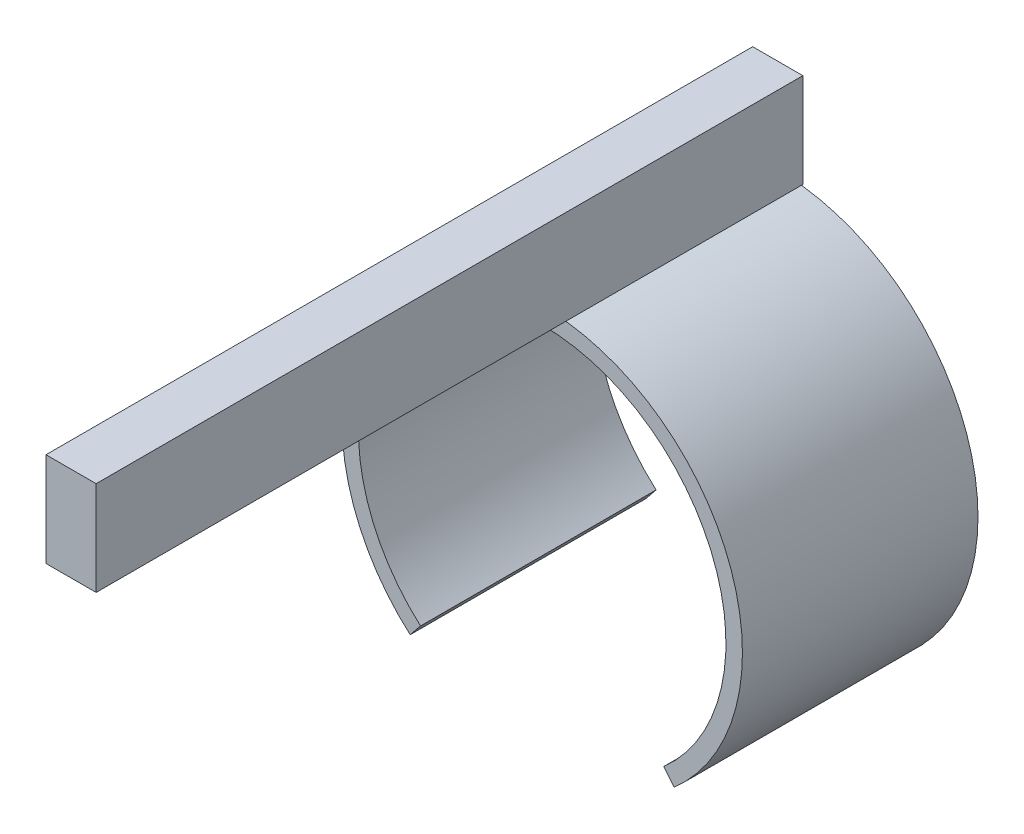
SolidWorks part; units mm, degrees
ref_plane "Front Plane" through (0, 0, 0) normal (0, 0, 1) x (1, 0, 0)
ref_plane "Top Plane" through (0, 0, 0) normal (0, 1, 0) x (1, 0, 0)
ref_plane "Right Plane" through (0, 0, 0) normal (1, 0, 0) x (0, 0, -1)
sketch "Sketch1" plane through (0, 0, 0) normal (0, 0, 1) x (1, 0, 0)
  circle A0 centre (0, 0) radius 3.9
  circle A1 centre (0, 0) radius 4.25
  dimension "D1" = 8.5
extrude "Boss-Extrude1" add sketch "Sketch1" along normal blind 5
sketch "Sketch2" plane through (0, 0, 5) normal (0, 0, 1) x (1, 0, 0)
  line L0 (-0.0022, 0.2598) -> (-0.0022, -6.2776) construction
  line L5 (-0.0022, 0.2598) -> (-3.8526, -4.4896)
  line L6 (-0.0022, 0.2598) -> (3.8481, -4.4896)
  arc A6 (-3.8526, -4.4896) -> (-0.0022, -6.2776) centre (-1.0334, -3.4584) ccw
  arc A7 (3.8481, -4.4896) -> (-0.0022, -6.2776) centre (1.029, -3.4584) cw
extrude "Cut-Extrude4" cut sketch "Sketch2" against normal blind 5
ref_plane "Plane1" through (0, 4.25, 0) normal (0, 1, 0) x (1, 0, 0)
sketch "Sketch3" plane through (0, 4.25, 0) normal (0, 1, 0) x (1, 0, 0)
  line L0 (4.25, 0) -> (-4.25, 0) construction
  line L1 (-0.5321, 0) -> (0.5321, 0)
  line L2 (-0.5321, 0) -> (-0.5321, -5)
  line L3 (-0.5321, -5) -> (0.5321, -5)
  line L4 (0.5321, 0) -> (0.5321, -5)
  line L5 (-4.25, -5) -> (4.25, -5) construction
  point P8 (0, 0)
extrude "Boss-Extrude2" add sketch "Sketch3" along normal blind 2 separate body
sketch "Sketch4" plane through (0, 0, 5) normal (0, 0, 1) x (1, 0, 0)
  line L4 (-0.5321, 4.25) -> (0.5321, 4.25)
  line L5 (0.5321, 4.25) -> (0.5321, 6.25)
  line L6 (0.5321, 6.25) -> (-0.5321, 6.25)
  line L7 (-0.5321, 6.25) -> (-0.5321, 4.25)
  line L8 (-0.5321, 4.25) -> (0.5321, 4.25)
  line L9 (0.5321, 4.25) -> (0.5321, 6.25)
  line L10 (0.5321, 6.25) -> (-0.5321, 6.25)
  line L11 (-0.5321, 6.25) -> (-0.5321, 4.25)
  dimension "D1" = 0
extrude "Boss-Extrude3" add sketch "Sketch4" along normal blind 10
